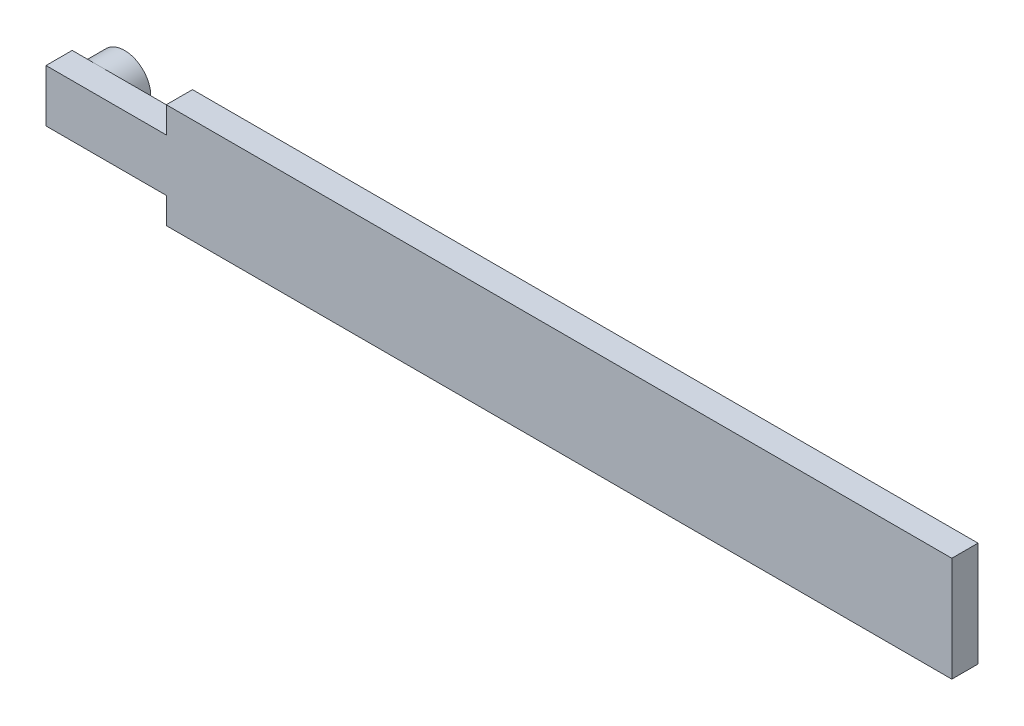
SolidWorks part; units mm, degrees
ref_plane "Front Plane" through (0, 0, 0) normal (0, 0, 1) x (1, 0, 0)
ref_plane "Top Plane" through (0, 0, 0) normal (0, 1, 0) x (1, 0, 0)
ref_plane "Right Plane" through (0, 0, 0) normal (1, 0, 0) x (0, 0, -1)
sketch "Sketch1" plane through (0, 0, 0) normal (0, 0, 1) x (1, 0, 0)
  line L0 (-75, -10) -> (75, -10)
  line L1 (-75, -10) -> (-75, -5)
  line L2 (75, -10) -> (75, 10)
  line L3 (-75, 10) -> (75, 10)
  line L4 (-75, -10) -> (75, 10) construction
  line L5 (75, -10) -> (-75, 10) construction
  line L6 (-75, -5) -> (-97.9701, -5)
  line L8 (-97.9701, -5) -> (-97.9701, 5)
  line L9 (-75, 5) -> (-97.9701, 5)
  line L12 (-75, 5) -> (-75, 10)
  circle A0 centre (-92.9701, 0) radius 5
  point P1 (0, 0)
  point P2 (-75, 0)
extrude "Boss-Extrude1" add sketch "Sketch1" along normal blind 5 contours L9 L8 L6 L1 L0 L2 L3 L12
sketch "Sketch2" plane through (0, 0, 0) normal (0, 0, -1) x (-1, 0, 0)
  line L0 (97.9701, -5) -> (97.9701, 5) construction
  circle A0 centre (92.9701, 0) radius 5
  point P2 (0, 0)
  dimension "D1" = 5
extrude "Boss-Extrude2" add sketch "Sketch2" along normal blind 5
